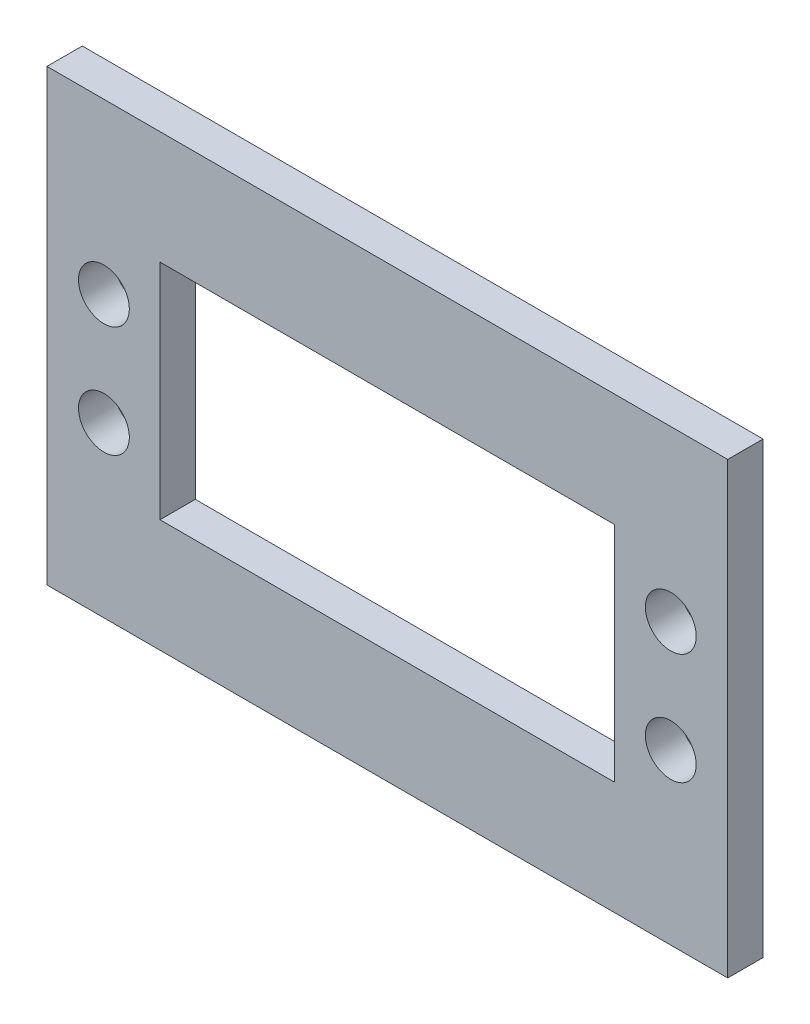
SolidWorks part; units mm, degrees
ref_plane "Front" through (0, 0, 0) normal (0, 0, 1) x (1, 0, 0)
ref_plane "Top" through (0, 0, 0) normal (0, 1, 0) x (1, 0, 0)
ref_plane "Right" through (0, 0, 0) normal (1, 0, 0) x (0, 0, -1)
sketch "Sketch1" plane through (0, 0, 0) normal (0, 0, 1) x (1, 0, 0)
  line L0 (-10.16, -10.16) -> (-10.16, 30.226)
  line L1 (0, 0) -> (40.894, 0)
  line L2 (0, 0) -> (0, 20.066)
  line L3 (0, 20.066) -> (40.894, 20.066)
  line L4 (40.894, 0) -> (40.894, 20.066)
  line L5 (-10.16, 30.226) -> (51.054, 30.226)
  line L6 (51.054, -10.16) -> (51.054, 30.226)
  line L7 (-10.16, -10.16) -> (51.054, -10.16)
  dimension "D1" = 40.894
  dimension "D2" = 20.066
  dimension "D3" = 10.16
extrude "Boss-Extrude1" add sketch "Sketch1" along normal blind 3.175
sketch "Sketch2" plane through (0, 0, 3.175) normal (0, 0, 1) x (1, 0, 0)
  line L0 (20.447, 30.226) -> (20.447, -10.16) construction
  line L1 (51.054, 30.226) -> (-10.16, 30.226) construction
  line L2 (-10.16, -10.16) -> (51.054, -10.16) construction
  line L3 (-10.16, 10.033) -> (51.054, 10.033) construction
  line L4 (-10.16, 30.226) -> (-10.16, -10.16) construction
  line L5 (51.054, -10.16) -> (51.054, 30.226) construction
  line L6 (0, 20.066) -> (0, 0) construction
  circle A0 centre (-5.04, 15.033) radius 2.286
  circle A1 centre (-5.04, 5.033) radius 2.286
  circle A2 centre (45.934, 5.033) radius 2.286
  circle A3 centre (45.934, 15.033) radius 2.286
  dimension "D1" = 4.572
  dimension "D2" = 5.04
  dimension "D3" = 5
extrude "Cut-Extrude1" cut sketch "Sketch2" against normal through all
